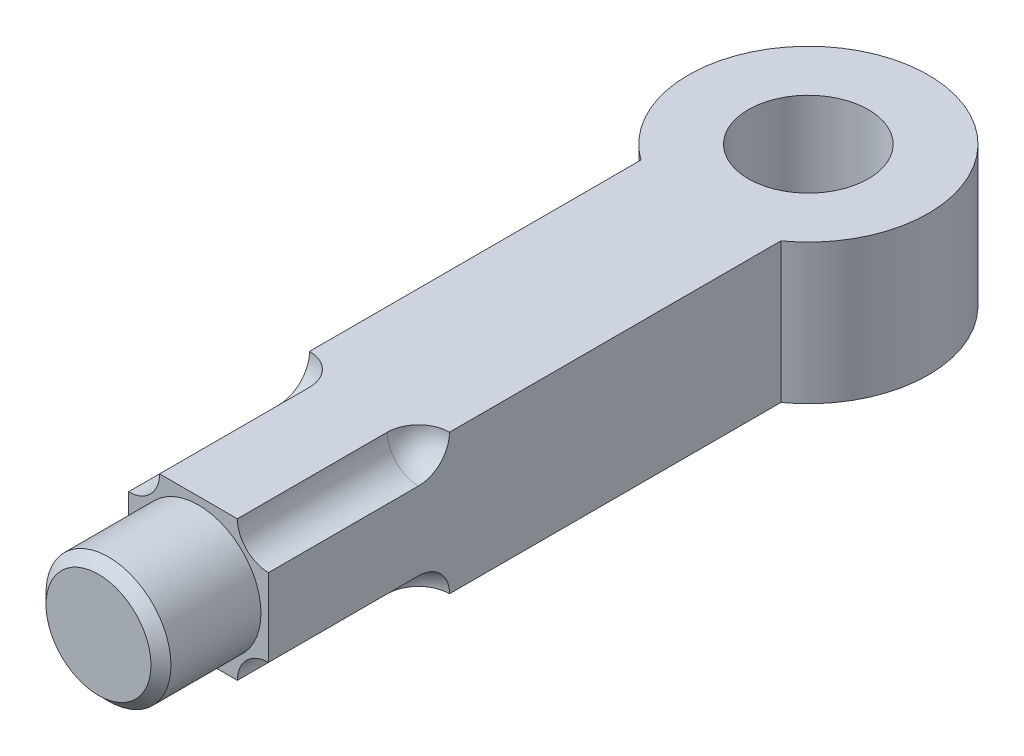
SolidWorks part; units mm, degrees
ref_plane "Front Plane" through (0, 0, 0) normal (0, 0, 1) x (1, 0, 0)
ref_plane "Top Plane" through (0, 0, 0) normal (0, 1, 0) x (1, 0, 0)
ref_plane "Right Plane" through (0, 0, 0) normal (1, 0, 0) x (0, 0, -1)
sketch "Sketch1" plane through (0, 0, 0) normal (0, 1, 0) x (1, 0, 0)
  circle A0 centre (0, 0) radius 12
  circle A1 centre (0, 0) radius 24
  dimension "D1" = 48
  dimension "D2" = 24
extrude "Boss-Extrude1" add sketch "Sketch1" along normal mid plane 28
ref_plane "Plane1" through (0, 0, 122) normal (0, 0, 1) x (1, 0, 0)
sketch "Sketch2" plane through (0, 0, 122) normal (0, 0, 1) x (1, 0, 0)
  line L1 (14, -14) -> (-14, -14)
  line L2 (14, -14) -> (14, 14)
  line L3 (14, 14) -> (-14, 14)
  line L4 (-14, -14) -> (-14, 14)
  line L5 (14, -14) -> (-14, 14) construction
  line L6 (14, 14) -> (-14, -14) construction
  point P0 (0, 0)
  dimension "D1" = 28
  dimension "D2" = 28
extrude "Boss-Extrude2" add sketch "Sketch2" against normal up to next
sketch "Sketch3" plane through (14, 0, 0) normal (1, 0, 0) x (0, 0, -1)
  line L0 (-122, 14) -> (-122, 7.78)
  line L1 (-122, 15.4) -> (-122, -15.4) construction
  line L2 (-122, 7.78) -> (-92, 7.78)
  line L4 (-19.4936, 14) -> (-122, 14) construction
  line L5 (-122, 14) -> (-85.78, 14)
  arc A0 (-92, 7.78) -> (-85.78, 14) centre (-92, 14) ccw
  dimension "D1" = 6.22
  dimension "D2" = 0
  dimension "D3" = 30
  dimension "D4" = 36.22
revolve "Cut-Revolve1" cut sketch "Sketch3" angle 360 about axis through (14, 14, -500000) along (0, 0, 1)
mirror "Mirror1" about plane through (0, 0, 0) normal (1, 0, 0) of "Cut-Revolve1"
mirror "Mirror2" about plane through (0, 0, 0) normal (0, 1, 0) of "Mirror1", "Cut-Revolve1"
sketch "Sketch4" plane through (0, 0, 122) normal (0, 0, 1) x (1, 0, 0)
  circle A0 centre (0, 0) radius 12.5
  dimension "D1" = 25
extrude "Boss-Extrude3" add sketch "Sketch4" along normal blind 20
chamfer "Chamfer1" distance 2 angle 45 1 edges at (12.5, 0, 142)
